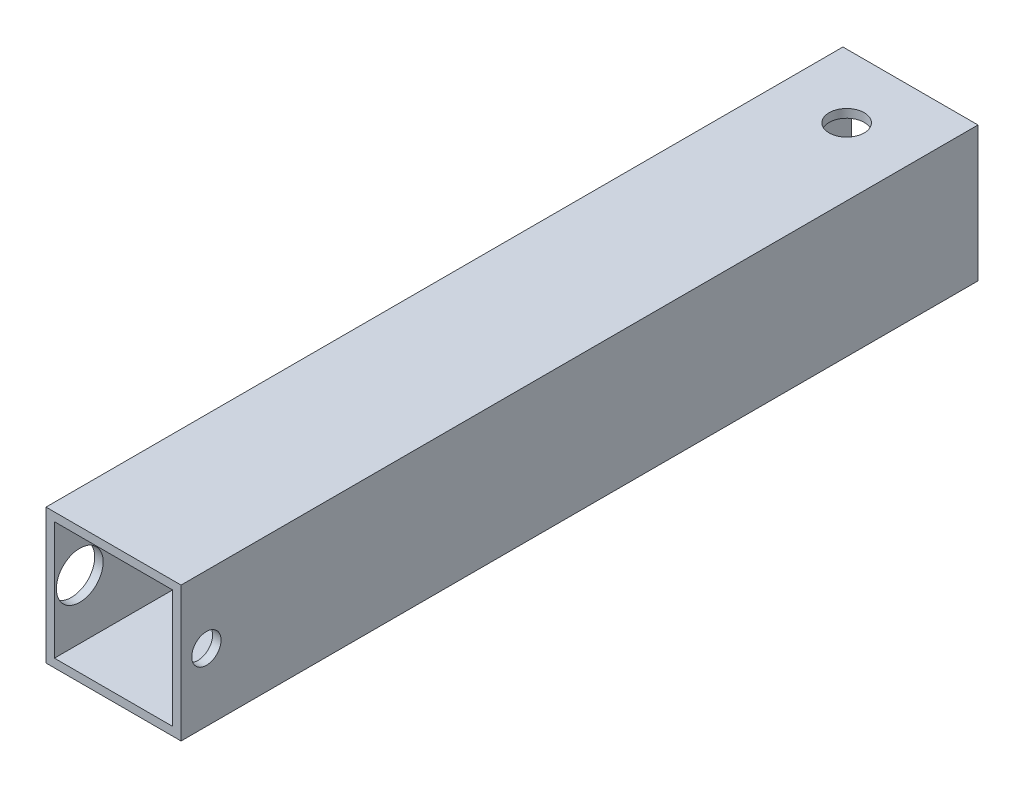
SolidWorks part; units mm, degrees
ref_plane "Front Plane" through (0, 0, 0) normal (0, 0, 1) x (1, 0, 0)
ref_plane "Top Plane" through (0, 0, 0) normal (0, 1, 0) x (1, 0, 0)
ref_plane "Right Plane" through (0, 0, 0) normal (1, 0, 0) x (0, 0, -1)
sketch "Sketch1" plane through (0, 0, 0) normal (0, 0, 1) x (1, 0, 0)
  line L1 (-12.7, -12.7) -> (12.7, -12.7)
  line L2 (-12.7, -12.7) -> (-12.7, 12.7)
  line L3 (-12.7, 12.7) -> (12.7, 12.7)
  line L4 (12.7, -12.7) -> (12.7, 12.7)
  line L5 (-12.7, -12.7) -> (12.7, 12.7) construction
  line L6 (-12.7, 12.7) -> (12.7, -12.7) construction
  point P0 (0, 0)
  dimension "D1" = 25.4
  dimension "D2" = 25.4
extrude "Boss-Extrude1" add sketch "Sketch1" along normal mid plane 149.86
shell "Shell1" thickness 1.5875
hole_wizard "CBORE for M5 SHCS1" positions "Sketch3" profile "Sketch2" counterbore size "M5" standard "ANSI Metric" end condition through all
sketch "Sketch3" plane through (-12.7, 0, 0) normal (-1, 0, 0) x (0, 0, 1)
  line L2 (74.93, 12.7) -> (74.93, -12.7) construction
  point P0 (70.1675, 0)
  dimension "D1" = 4.7625
sketch "Sketch2" plane through (-12.7, 0, 70.1675) normal (0, 1, 0) x (0, 0, 1)
  line L0 (0, 0) -> (0, 25.4)
  line L1 (0, 25.4) -> (2.75, 25.4)
  line L3 (2.75, 25.4) -> (2.75, 5)
  line L4 (2.75, 5) -> (4.4, 5)
  line L5 (4.4, 5) -> (4.4, 0)
  line L7 (4.4, 0) -> (0, 0)
  line L11 (0, -6.35) -> (0, 107.95) construction
  dimension "Thru Hole Dia." = 5.5
  dimension "Thru Hole Depth" = 25.4
  dimension "C'Bore Dia." = 8.8
  dimension "C'Bore Depth" = 5
hole_wizard "M6 Clearance Hole1" positions "Sketch5" profile "Sketch4" hole size "M6" standard "ANSI Metric" end condition through all
sketch "Sketch5" plane through (0, -12.7, 0) normal (0, -1, 0) x (-1, 0, 0)
  line L0 (12.7, 74.93) -> (-12.7, 74.93) construction
  point P0 (0, 62.93)
  dimension "D1" = 12
sketch "Sketch4" plane through (0, -12.7, -62.93) normal (1, 0, 0) x (0, 0, -1)
  line L0 (0, 0) -> (0, 25.4)
  line L1 (0, 25.4) -> (3.3, 25.4)
  line L2 (3.3, 25.4) -> (3.3, 0)
  line L5 (3.3, 0) -> (0, 0)
  line L11 (0, -6.35) -> (0, 107.95) construction
  dimension "Thru Hole Dia." = 6.6
  dimension "Thru Hole Depth" = 25.4
